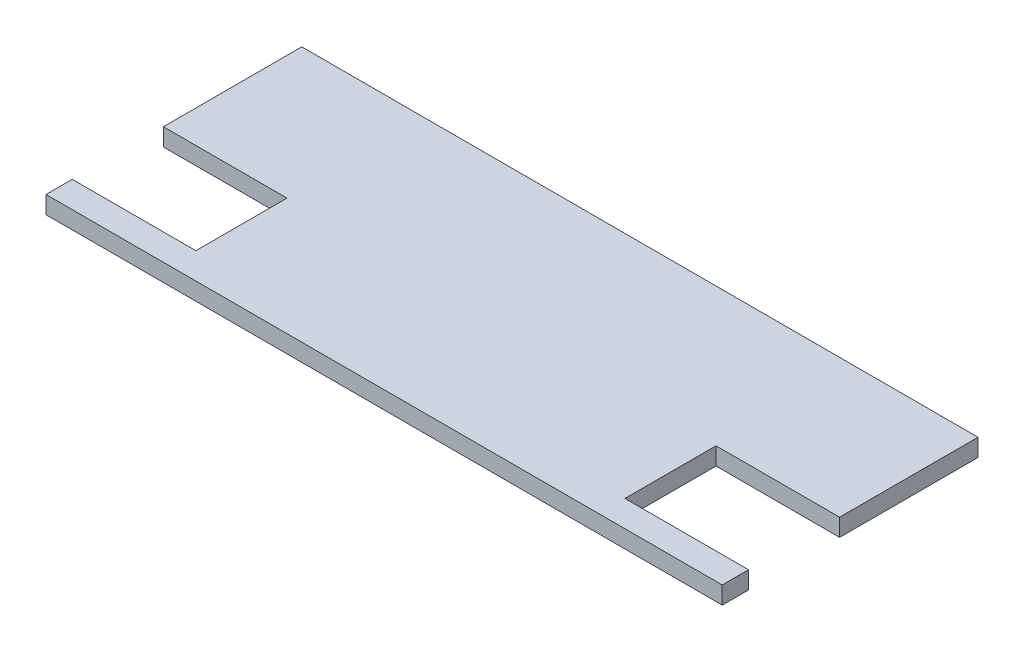
SolidWorks part; units mm, degrees
ref_plane "Alzado" through (0, 0, 0) normal (0, 0, 1) x (1, 0, 0)
ref_plane "Planta" through (0, 0, 0) normal (0, 1, 0) x (1, 0, 0)
ref_plane "Vista lateral" through (0, 0, 0) normal (1, 0, 0) x (0, 0, -1)
sketch "Croquis1" plane through (0, 0, 0) normal (0, 1, 0) x (1, 0, 0)
  line L1 (-96.5, -36.5) -> (96.5, -36.5)
  line L2 (-96.5, -36.5) -> (-96.5, 36.5)
  line L3 (-96.5, 36.5) -> (96.5, 36.5)
  line L4 (96.5, -36.5) -> (96.5, 36.5)
  line L5 (-96.5, -36.5) -> (96.5, 36.5) construction
  line L6 (-96.5, 36.5) -> (96.5, -36.5) construction
  line L7 (-96.5, -29) -> (-61.23, -29)
  line L8 (-96.5, -29) -> (-96.5, -3)
  line L9 (-96.5, -3) -> (-61.23, -3)
  line L10 (-61.23, -29) -> (-61.23, -3)
  line L11 (96.5, -29) -> (61.23, -29)
  line L12 (96.5, -29) -> (96.5, -3)
  line L13 (96.5, -3) -> (61.23, -3)
  line L14 (61.23, -29) -> (61.23, -3)
  point P0 (0, 0)
  dimension "D1" = 193
  dimension "D2" = 73
  dimension "D3" = 7.5
  dimension "D4" = 26
  dimension "D5" = 35.27
  dimension "D6" = 35.27
extrude "Saliente-Extruir1" add sketch "Croquis1" along normal blind 5 contours L11 L14 L13 L4 L3 L2 L9 L10 L7 L1
